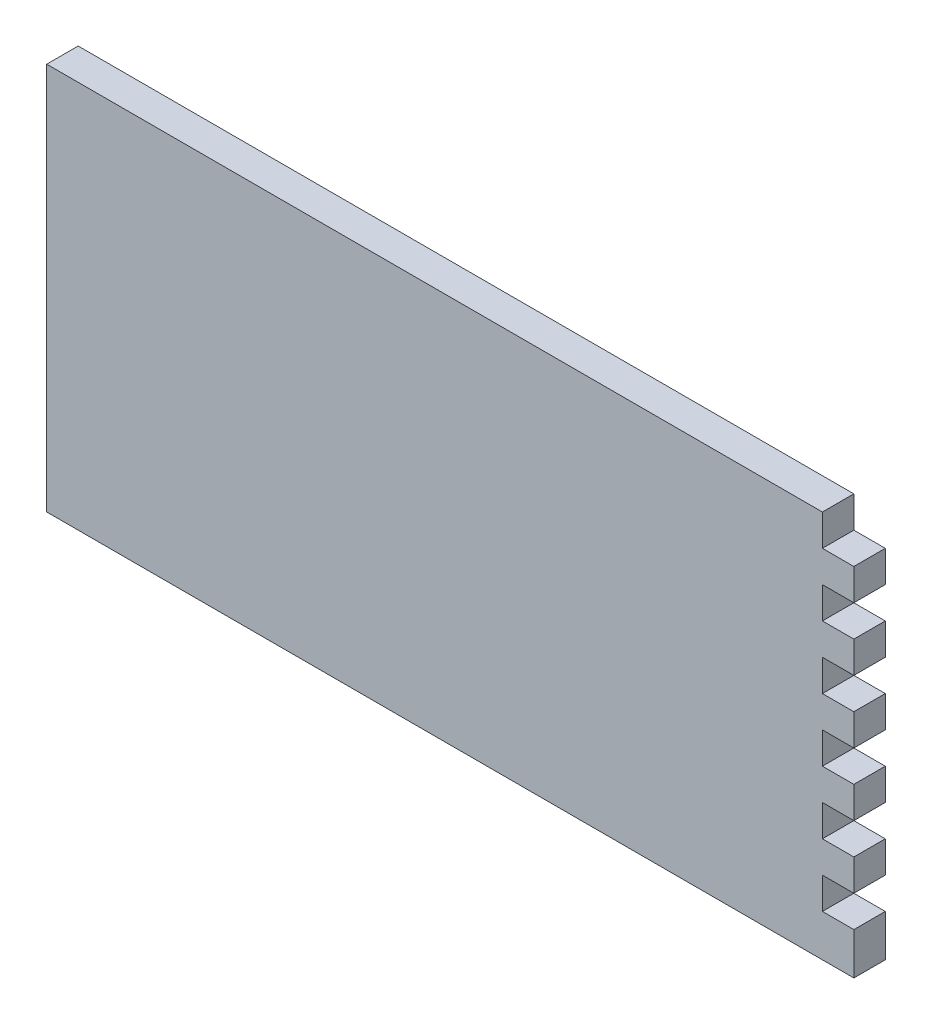
SolidWorks part; units mm, degrees
ref_plane "Front Plane" through (0, 0, 0) normal (0, 0, 1) x (1, 0, 0)
ref_plane "Top Plane" through (0, 0, 0) normal (0, 1, 0) x (1, 0, 0)
ref_plane "Right Plane" through (0, 0, 0) normal (1, 0, 0) x (0, 0, -1)
sketch "Sketch1" plane through (0, 0, 0) normal (0, 1, 0) x (1, 0, 0)
  line L0 (0, 0) -> (-192.5, 0)
  line L1 (-192.5, 0) -> (-192.5, 7.5)
  line L2 (-192.5, 7.5) -> (0, 7.5)
  line L3 (0, 7.5) -> (0, 0)
extrude "Boss-Extrude1" add sketch "Sketch1" along normal blind 92.5
sketch "Sketch2" plane through (0, 92.5, 0) normal (0, 1, 0) x (1, 0, 0)
  line L0 (0, 0) -> (-7.5, 0)
  line L1 (-192.5, 0) -> (0, 0) construction
  line L6 (0, 0) -> (0, 7.5)
  line L7 (0, 7.5) -> (-192.5, 7.5)
  line L8 (-192.5, 7.5) -> (-192.5, 0)
  line L9 (-192.5, 0) -> (0, 0)
  line L10 (0, 0) -> (0, 7.5)
  line L11 (0, 7.5) -> (-192.5, 7.5)
  line L12 (-192.5, 7.5) -> (-192.5, 0)
  line L13 (-192.5, 0) -> (-7.5, 0)
  dimension "D1" = 0
sketch "Sketch4" plane through (0, 0, 0) normal (0, 0, 1) x (1, 0, 0)
  line L0 (0, 92.5) -> (-7.5, 92.5)
  line L1 (0, 92.5) -> (0, 0) construction
  line L2 (-192.5, 92.5) -> (0, 92.5) construction
  line L3 (-7.5, 92.5) -> (-7.5, 85)
  line L4 (-7.5, 85) -> (0, 85)
  line L5 (0, 85) -> (0, 77.5)
  line L6 (-7.5, 70) -> (0, 70)
  line L7 (0, 70) -> (0, 62.5)
  line L8 (0, 77.5) -> (-7.5, 77.5)
  line L9 (-7.5, 77.5) -> (-7.5, 70)
  line L10 (-7.5, 55) -> (0, 55)
  line L11 (0, 62.5) -> (-7.5, 62.5)
  line L12 (-7.5, 62.5) -> (-7.5, 55)
  line L13 (0, 55) -> (0, 47.5)
  line L14 (-7.5, 40) -> (0, 40)
  line L15 (0, 32.5) -> (-7.5, 32.5)
  line L16 (-7.5, 10) -> (0, 10)
  line L17 (0, 25) -> (0, 17.5)
  line L18 (-7.5, 32.5) -> (-7.5, 25)
  line L19 (0, 17.5) -> (-7.5, 17.5)
  line L20 (-7.5, 25) -> (0, 25)
  line L21 (-7.5, 47.5) -> (-7.5, 40)
  line L22 (0, 10) -> (0, 2.5)
  line L23 (0, 47.5) -> (-7.5, 47.5)
  line L24 (0, 40) -> (0, 32.5)
  line L25 (-7.5, 17.5) -> (-7.5, 10)
  line L26 (0, 92.5) -> (0, 10)
  line M14 (0, 0) -> (0, 92.5)
  line M15 (0, 92.5) -> (-192.5, 92.5)
extrude "Cut-Extrude1" cut sketch "Sketch4" against normal blind 92.5 contours L3 L4 M14 M15 | L8 L9 L6 M14 | L11 L12 L10 M14 | L23 L21 L14 M14 | L18 L20 L15 M14 | L19 L25 L16 M14
sketch "Sketch5" plane through (0, 0, 0) normal (0, 0, 1) x (1, 0, 0)
  line L0 (0, 81.25) -> (-7.5, 81.25)
  line L1 (0, 85) -> (0, 77.5) construction
  circle A0 centre (-3.75, 81.25) radius 2.5
